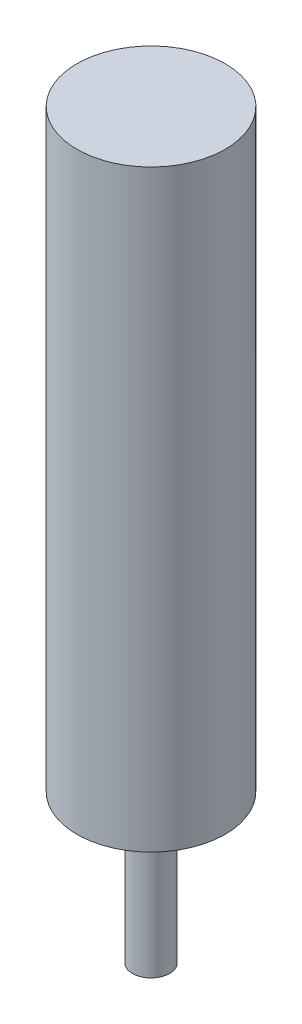
SolidWorks part; units mm, degrees
material "Rubber"
ref_plane "Front Plane" through (0, 0, 0) normal (0, 0, 1) x (1, 0, 0)
ref_plane "Top Plane" through (0, 0, 0) normal (0, 1, 0) x (1, 0, 0)
ref_plane "Right Plane" through (0, 0, 0) normal (1, 0, 0) x (0, 0, -1)
sketch "Sketch1" plane through (0, 0, 0) normal (0, 0, 1) x (1, 0, 0)
  line L0 (0, 0) -> (0, 63.5) construction
  line L1 (0, 63.5) -> (6.35, 63.5)
  line L2 (6.35, 63.5) -> (6.35, 12.7)
  line L3 (6.35, 12.7) -> (1.5875, 12.7)
  line L4 (1.5875, 12.7) -> (1.5875, 0)
  line L5 (1.5875, 0) -> (0, 0)
  line L6 (0, 0) -> (0, 63.5)
  dimension "D1" = 6.35
  dimension "D2" = 1.5875
  dimension "D3" = 50.8
  dimension "D4" = 12.7
revolve "Revolve1" add sketch "Sketch1" angle 360 about L0
